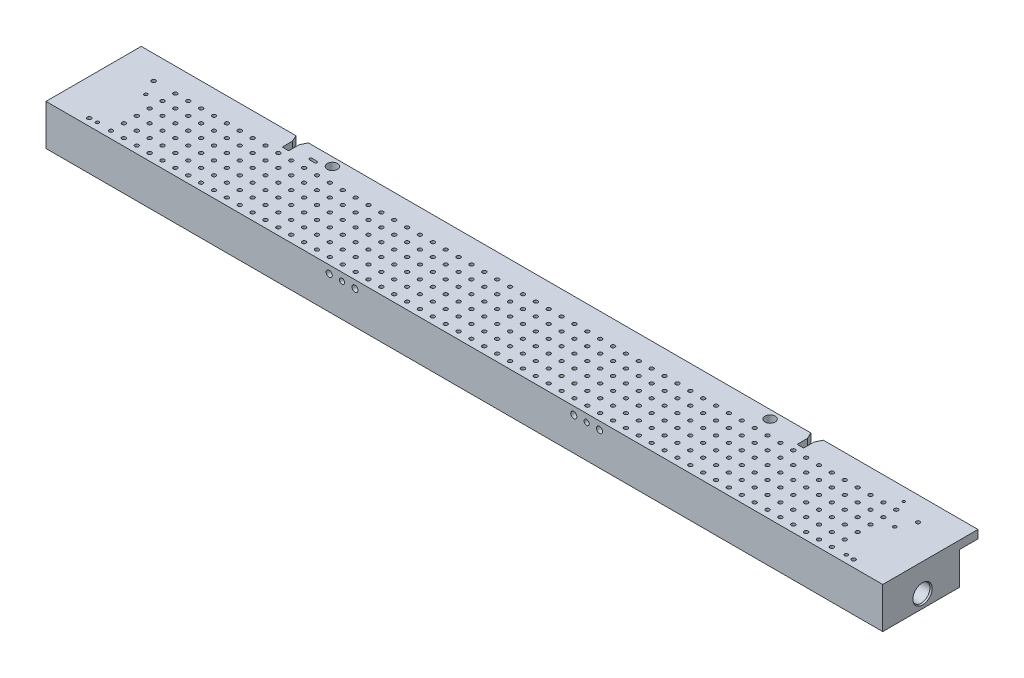
SolidWorks part; units mm, degrees
ref_plane "Front Plane" through (0, 0, 0) normal (0, 0, 1) x (1, 0, 0)
ref_plane "Top Plane" through (0, 0, 0) normal (0, 1, 0) x (1, 0, 0)
ref_plane "Right Plane" through (0, 0, 0) normal (1, 0, 0) x (0, 0, -1)
sketch "Sketch1" plane through (0, 0, 0) normal (0, 1, 0) x (1, 0, 0)
  line L1 (-55.7213, 28.6477) -> (594.2787, 28.6477)
  line L2 (-55.7213, 28.6477) -> (-55.7213, -85.6523)
  line L3 (-55.7213, -85.6523) -> (594.2787, -85.6523)
  line L4 (594.2787, 28.6477) -> (594.2787, -85.6523)
  dimension "D1" = 650
  dimension "D2" = 114.3
extrude "Boss-Extrude1" add sketch "Sketch1" against normal blind 31.75
hole_wizard "Hole2" positions "Sketch5" profile "Sketch4" legacy
sketch "Sketch5" plane through (0, 0, 0) normal (0, 1, 0) x (1, 0, 0)
  line L0 (-55.7213, 28.6477) -> (-55.7213, -85.6523) construction
  line L1 (-55.7213, -85.6523) -> (594.2787, -85.6523) construction
  point P0 (99.2787, -18.1523)
  point P2 (439.2787, -18.1523)
  dimension "D1" = 155
  dimension "D2" = 340
  dimension "D3" = 67.5
  dimension "D4" = 67.5
sketch "Sketch4" plane through (99.2787, 0, 18.1523) normal (1, 0, 0) x (0, 0, 1)
  line L0 (0, 0) -> (0, 15.875)
  line L1 (0, 15.875) -> (3.9815, 15.875)
  line L2 (3.9815, 15.875) -> (3.9815, 0)
  line L3 (3.9815, 0) -> (0, 0)
  line L4 (0, 110) -> (0, -10) construction
  dimension "Diameter" = 7.9629
  dimension "Depth" = 15.875
hole_wizard "Hole4" positions "Sketch12" profile "Sketch11" legacy
sketch "Sketch12" plane through (0, 0, 0) normal (0, 1, 0) x (1, 0, 0)
  line L0 (-55.7213, -85.6523) -> (594.2787, -85.6523) construction
  line L1 (269.2787, 45.076) -> (269.2787, -110.0283) construction
  point P0 (69.2787, -22.1523)
  point P2 (469.2787, -22.1523)
  dimension "D1" = 200
  dimension "D2" = 200
  dimension "D3" = 63.5
  dimension "D4" = 63.5
sketch "Sketch11" plane through (69.2787, 0, 22.1523) normal (1, 0, 0) x (0, 0, 1)
  line L0 (0, 0) -> (0, 15.875)
  line L1 (0, 15.875) -> (2.5, 15.875)
  line L2 (2.5, 15.875) -> (2.5, 0)
  line L3 (2.5, 0) -> (0, 0)
  line L4 (0, 110) -> (0, -10) construction
  dimension "Diameter" = 5
  dimension "Depth" = 15.875
hole_wizard "Hole6" positions "Sketch16" profile "Sketch15" legacy
sketch "Sketch16" plane through (0, 0, 0) normal (0, 1, 0) x (1, 0, 0)
  line L1 (-55.7213, -85.6523) -> (594.2787, -85.6523) construction
  line L2 (269.2787, -103.4746) -> (269.2787, 56.727) construction
  point P2 (-27.6213, -80.1523)
  point P4 (566.1787, -80.1523)
  point P22 (-27.6213, -30.1523)
  point P25 (566.1787, -30.1523)
  dimension "D1" = 296.9
  dimension "D2" = 296.9
  dimension "D3" = 55.5
  dimension "D5" = 5.5
  dimension "D6" = 5.5
sketch "Sketch15" plane through (-27.6213, 0, 80.1523) normal (1, 0, 0) x (0, 0, 1)
  line L0 (0, 0) -> (0, 5)
  line L1 (0, 5) -> (1.5, 5)
  line L2 (1.5, 5) -> (1.5, 0)
  line L3 (1.5, 0) -> (0, 0)
  line L4 (0, 110) -> (0, -10) construction
  dimension "Diameter" = 3
  dimension "Depth" = 5
hole_wizard "Hole7" positions "Sketch18" profile "Sketch17" legacy
sketch "Sketch18" plane through (0, 0, 0) normal (0, 1, 0) x (1, 0, 0)
  line L0 (-55.7213, -85.6523) -> (594.2787, -85.6523) construction
  line L1 (269.2787, 54.0915) -> (269.2787, -171.9418) construction
  point P0 (279.2787, -80.1523)
  dimension "D2" = 10
  dimension "D1" = 5.5
sketch "Sketch17" plane through (279.2787, 0, 80.1523) normal (1, 0, 0) x (0, 0, 1)
  line L0 (0, 0) -> (0, 30)
  line L1 (0, 30) -> (1.5, 30)
  line L2 (1.5, 30) -> (1.5, 0)
  line L3 (1.5, 0) -> (0, 0)
  line L4 (0, 110) -> (0, -10) construction
  dimension "Diameter" = 3
  dimension "Depth" = 30
sketch "Sketch19" plane through (0, 0, 0) normal (0, 1, 0) x (1, 0, 0)
  line L0 (277.7787, -80.1523) -> (50277.7787, -80.1523) construction
  line L1 (279.2787, -80.1523) -> (279.2787, 49919.8477) construction
  line L2 (269.2787, 97.4934) -> (269.2787, -133.194) construction
  circle A0 centre (279.2787, -80.1523) radius 1.5 construction
  dimension "D1" = 10
pattern_linear "LPattern2" count 28 spacing 10 along (1, 0, 0) count 6 spacing 10 along (0, 0, -1) of "Hole7"
hole_wizard "Hole12" positions "Sketch34" profile "Sketch33" legacy
sketch "Sketch34" plane through (0, 0, 0) normal (0, 1, 0) x (1, 0, 0)
  line L0 (-199722.2213, -80.1523) -> (250277.7787, -80.1523) construction
  line L1 (269.2787, 97.4934) -> (269.2787, -133.194) construction
  point P0 (269.2787, -80.1523)
sketch "Sketch33" plane through (269.2787, 0, 80.1523) normal (1, 0, 0) x (0, 0, 1)
  line L0 (0, 0) -> (0, 30)
  line L1 (0, 30) -> (1.5, 30)
  line L2 (1.5, 30) -> (1.5, 0)
  line L3 (1.5, 0) -> (0, 0)
  line L4 (0, 110) -> (0, -10) construction
  dimension "Diameter" = 3
  dimension "Depth" = 30
pattern_linear "LPattern3" count 29 spacing 10 along (-1, 0, 0) count 6 spacing 10 along (0, 0, -1) of "Hole12"
sketch "Sketch35" plane through (0, 0, 85.6523) normal (0, 0, 1) x (1, 0, 0)
  line L0 (269.2787, 71.714) -> (269.2787, -64.9274) construction
  line L1 (-55.7213, -31.75) -> (-55.7213, 0) construction
  dimension "D1" = 325
hole_wizard "Hole13" positions "Sketch37" profile "Sketch36" legacy
sketch "Sketch37" plane through (0, 0, 85.6523) normal (0, 0, 1) x (1, 0, 0)
  line L0 (269.2787, 71.714) -> (269.2787, -64.9274) construction
  line L1 (-199722.2213, 0) -> (250277.7787, 0) construction
  point P0 (184.2787, -6)
  point P2 (164.2787, -6)
  point P4 (374.2787, -6)
  point P6 (354.2787, -6)
  dimension "D1" = 105
  dimension "D2" = 85
  dimension "D3" = 105
  dimension "D4" = 85
  dimension "D5" = 6
  dimension "D6" = 6
  dimension "D7" = 6
  dimension "D8" = 6
sketch "Sketch36" plane through (184.2787, -6, 85.6523) normal (1, 0, 0) x (0, -1, 0)
  line L0 (0, 0) -> (0, 12)
  line L1 (0, 12) -> (2.3813, 12)
  line L2 (2.3813, 12) -> (2.3813, 0)
  line L3 (2.3813, 0) -> (0, 0)
  line L4 (0, 110) -> (0, -10) construction
  dimension "Diameter" = 4.7625
  dimension "Depth" = 12
hole_wizard "#10-32 Tapped Hole1" positions "Sketch40" profile "Sketch38" tap size "#10-32" standard "ANSI Inch"
sketch "Sketch40" plane through (0, 0, 85.6523) normal (0, 0, 1) x (1, 0, 0)
  line L0 (269.2787, 71.714) -> (269.2787, -64.9274) construction
  line L1 (-199722.2213, 0) -> (250277.7787, 0) construction
  point P0 (174.2787, -6)
  point P2 (364.2787, -6)
  dimension "D1" = 95
  dimension "D2" = 95
  dimension "D3" = 6
  dimension "D4" = 6
sketch "Sketch38" plane through (174.2787, -6, 85.6523) normal (1, 0, 0) x (0, -1, 0)
  line L0 (0, 0) -> (0, 16.4533)
  line L1 (0, 16.4533) -> (2.0193, 15.24)
  line L2 (2.0193, 15.24) -> (2.0193, 0)
  line L5 (2.0193, 0) -> (0, 0)
  line L10 (0, 16.4533) -> (-2.0193, 15.24) construction
  line L11 (0, -6.35) -> (0, 107.95) construction
  dimension "Tap Drill Dia." = 4.0386
  dimension "Tap Drill Depth" = 15.24
  dimension "Drill Angle" = 118
cosmetic thread "Hole Thread1" parameters "D1"=12.7, "D2"=4.826
cosmetic thread "Hole Thread2" parameters "D1"=12.7, "D2"=4.826
sketch "Sketch41" plane through (0, -31.75, 0) normal (0, -1, 0) x (1, 0, 0)
  line L1 (-15.7213, 81.1523) -> (554.2787, 81.1523)
  line L2 (-15.7213, 81.1523) -> (-15.7213, 26.1523)
  line L3 (-15.7213, 26.1523) -> (554.2787, 26.1523)
  line L4 (554.2787, 81.1523) -> (554.2787, 26.1523)
  line L5 (-55.7213, 85.6523) -> (594.2787, 85.6523) construction
  line L6 (-55.7213, -28.6477) -> (-55.7213, 85.6523) construction
  line L7 (594.2787, 85.6523) -> (594.2787, -28.6477) construction
  dimension "D1" = 4.5
  dimension "D2" = 55
  dimension "D3" = 40
  dimension "D4" = 40
sketch "Sketch51" plane through (594.2787, 0, 0) normal (1, 0, 0) x (0, 0, -1)
  line L0 (-85.6523, -31.75) -> (28.6477, -31.75) construction
  line L1 (28.6477, 0) -> (-11.6523, 0)
  line L2 (28.6477, 0) -> (28.6477, -31.75)
  line L3 (28.6477, -31.75) -> (-11.6523, -31.75)
  line L4 (-11.6523, 0) -> (-11.6523, -31.75)
  dimension "D1" = 40.3
extrude "Cut-Extrude8" cut sketch "Sketch51" against normal blind 40000
sketch "Sketch52" plane through (594.2787, 0, 0) normal (1, 0, 0) x (0, 0, -1)
  line L1 (-11.6523, -31.75) -> (-21.6523, -31.75)
  line L2 (-11.6523, -31.75) -> (-11.6523, -6.35)
  line L3 (-11.6523, -6.35) -> (-21.6523, -6.35)
  line L4 (-21.6523, -31.75) -> (-21.6523, -6.35)
  dimension "D1" = 10
  dimension "D2" = 25.4
extrude "Cut-Extrude9" cut sketch "Sketch52" against normal blind 40000
sketch "Sketch55" plane through (-55.7213, 0, 0) normal (-1, 0, 0) x (0, 0, 1)
  line L0 (21.6523, -31.75) -> (85.6523, -31.75) construction
  line L1 (21.6523, -6.35) -> (25.1523, -6.35)
  line L2 (21.6523, -6.35) -> (21.6523, -31.75)
  line L3 (21.6523, -31.75) -> (25.1523, -31.75)
  line L4 (25.1523, -6.35) -> (25.1523, -31.75)
  dimension "D1" = 3.5
extrude "Cut-Extrude10" cut sketch "Sketch55" against normal blind 40000
sketch "Sketch56" plane through (594.2787, 0, 0) normal (1, 0, 0) x (0, 0, -1)
  line L1 (-25.1523, -31.75) -> (-26.1523, -31.75)
  line L2 (-25.1523, -31.75) -> (-25.1523, -6.35)
  line L3 (-25.1523, -6.35) -> (-26.1523, -6.35)
  line L4 (-26.1523, -31.75) -> (-26.1523, -6.35)
  dimension "D1" = 25.4
  dimension "D2" = 1
extrude "Cut-Extrude11" cut sketch "Sketch56" against normal blind 40000
sketch "Sketch57" plane through (0, -31.75, 0) normal (0, -1, 0) x (-1, 0, 0)
  line L1 (15.7213, -81.1523) -> (-554.2787, -81.1523)
  line L2 (15.7213, -81.1523) -> (15.7213, -30.3716)
  line L3 (15.7213, -30.3716) -> (-554.2787, -30.3716)
  line L4 (-554.2787, -81.1523) -> (-554.2787, -30.3716)
extrude "Cut-Extrude12" cut sketch "Sketch57" against normal blind 10
sketch "Sketch58" plane through (0, -31.75, 0) normal (0, -1, 0) x (-1, 0, 0)
  line L0 (-557.2787, -84.1523) -> (18.7213, -84.1523)
  line L1 (18.7213, -84.1523) -> (18.7213, -27.3716)
  line L3 (18.7213, -27.3716) -> (-557.2787, -27.3716)
  line L4 (-557.2787, -84.1523) -> (-557.2787, -27.3716)
  line L5 (15.7213, -30.3716) -> (-554.2787, -30.3716) construction
  dimension "D1" = 3
extrude "Cut-Extrude13" cut sketch "Sketch58" against normal blind 3.5
fillet "Fillet1" radius 3.18 8 edges at (554.2787, -25, 30.3716) (557.2787, -30, 27.3716) (554.2787, -25, 81.1523) (-15.7213, -25, 30.3716) (-15.7213, -25, 81.1523) (557.2787, -30, 84.1523) (-18.7213, -30, 84.1523) (-18.7213, -30, 27.3716)
sketch "Sketch60" plane through (0, -6.35, 0) normal (0, -1, 0) x (-1, 0, 0)
  line L0 (-594.2787, -11.6523) -> (55.7213, -11.6523) construction
  line L1 (-66.7787, -24.6523) -> (-71.7787, -24.6523)
  line L2 (-66.7787, -24.6523) -> (-66.7787, -11.6523)
  line L3 (-66.7787, -11.6523) -> (-71.7787, -11.6523)
  line L4 (-71.7787, -24.6523) -> (-71.7787, -11.6523)
extrude "Cut-Extrude17" cut sketch "Sketch60" against normal blind 10
sketch "Sketch61" plane through (0, -6.35, 0) normal (0, -1, 0) x (-1, 0, 0)
  line L0 (-594.2787, -11.6523) -> (-71.7787, -11.6523) construction
  line L1 (-466.7787, -24.6523) -> (-471.7787, -24.6523)
  line L2 (-466.7787, -24.6523) -> (-466.7787, -11.6523)
  line L3 (-466.7787, -11.6523) -> (-471.7787, -11.6523)
  line L4 (-471.7787, -24.6523) -> (-471.7787, -11.6523)
  circle A0 centre (-469.2787, -22.1523) radius 2.5 construction
  dimension "D2" = 2.5
  dimension "D1" = 2.5
  dimension "D3" = 5
extrude "Cut-Extrude18" cut sketch "Sketch61" against normal blind 10
chamfer "Chamfer3" distance 5 angle 25 1 edges at (66.7787, -3.175, 11.6523)
chamfer "Chamfer4" distance 5 angle 25 1 edges at (71.7787, -3.175, 11.6523)
chamfer "Chamfer5" distance 5 angle 25 1 edges at (471.7787, -3.175, 11.6523)
chamfer "Chamfer6" distance 5 angle 25 1 edges at (466.7787, -3.175, 11.6523)
hole_wizard "1/4 NPT Tapped Hole1" positions "Sketch65" profile "Sketch64" size "1/4" standard "ANSI Inch"
sketch "Sketch65" plane through (594.2787, 0, 0) normal (1, 0, 0) x (0, 0, -1)
  line L0 (-81.1523, -31.75) -> (-26.1523, -31.75) construction
  point P0 (-54.7527, -21.75)
  dimension "D1" = 10
sketch "Sketch64" plane through (594.2787, -21.75, 54.7527) normal (0, 1, 0) x (0, 0, -1)
  line L0 (0, 0) -> (0, 50.4123)
  line L1 (5.5626, 47.07) -> (0, 50.4123)
  line L2 (-5.5626, 47.07) -> (0, 50.4123) construction
  line L3 (5.5626, 47.07) -> (5.5626, 10.02)
  line L4 (5.5626, 10.02) -> (6.5909, 10.02)
  line L5 (6.5909, 10.02) -> (6.858, 1.0999)
  line L6 (6.858, 1.0999) -> (7.493, 0)
  line L7 (7.493, 0) -> (0, 0)
  line L8 (0, -6.35) -> (0, 107.95) construction
  line L9 (-6.858, 1.0999) -> (-7.493, 0) construction
  line L11 (-5.5626, 10.02) -> (-6.5909, 10.02) construction
  line L12 (-6.5909, 10.02) -> (-6.858, 1.0999) construction
  dimension "Tap Drill Dia." = 11.1252
  dimension "Tap Drill Depth" = 47.07
  dimension "Thread Dia." = 13.716
  dimension "Thread Angle" = 3.43
  dimension "Thread Depth" = 10.02
  dimension "C'Sink Dia." = 14.986
  dimension "C'Sink Angle" = 60
  dimension "Drill Angle" = 118
sketch "Sketch67" plane through (0, 0, 0) normal (0, 1, 0) x (1, 0, 0)
  line L0 (-55.7213, -85.6523) -> (594.2787, -85.6523) construction
  line L1 (269.2787, 97.4934) -> (269.2787, -133.194) construction
  line L2 (85.8787, -21.6523) -> (89.8787, -21.6523) construction
  line L3 (85.8787, -20.6523) -> (89.8787, -20.6523)
  line L4 (85.8787, -22.6523) -> (89.8787, -22.6523)
  circle A0 centre (546.6787, -21.6523) radius 1
  arc A1 (85.8787, -20.6523) -> (85.8787, -22.6523) centre (85.8787, -21.6523) ccw
  arc A2 (89.8787, -22.6523) -> (89.8787, -20.6523) centre (89.8787, -21.6523) ccw
  point P8 (87.8787, -21.6523)
  dimension "D1" = 64
  dimension "D3" = 181.4
  dimension "D2" = 277.4
extrude "Cut-Extrude19" cut sketch "Sketch67" against normal blind 5
hole_wizard "M3x0.5 Tapped Hole2" positions "Sketch73" profile "Sketch72" tap size "M3x0.5" standard "ANSI Metric"
sketch "Sketch73" plane through (0, 0, 0) normal (0, 1, 0) x (1, 0, 0)
  line L0 (269.2787, 97.4934) -> (269.2787, -133.194) construction
  line L2 (-55.7213, -85.6523) -> (594.2787, -85.6523) construction
  point P0 (-21.6213, -42.2053)
  point P8 (-21.6213, -79.8803)
  point P13 (560.1787, -42.2053)
  point P19 (560.1787, -79.8803)
  dimension "D1" = 290.9
  dimension "D2" = 5.772
  dimension "D3" = 43.447
  dimension "D4" = 290.9
  dimension "D5" = 5.772
  dimension "D6" = 43.447
sketch "Sketch72" plane through (-21.6213, 0, 42.2053) normal (1, 0, 0) x (0, 0, 1)
  line L0 (0, 0) -> (0, 10.7511)
  line L1 (0, 10.7511) -> (1.25, 10)
  line L2 (1.25, 10) -> (1.25, 0)
  line L5 (1.25, 0) -> (0, 0)
  line L10 (0, 10.7511) -> (-1.25, 10) construction
  line L11 (0, -6.35) -> (0, 107.95) construction
  dimension "Tap Drill Dia." = 2.5
  dimension "Tap Drill Depth" = 10
  dimension "Drill Angle" = 118
cosmetic thread "Hole Thread4" parameters "D1"=6, "D2"=3
cosmetic thread "Hole Thread5" parameters "D1"=6, "D2"=3
cosmetic thread "Hole Thread6" parameters "D1"=6, "D2"=3
cosmetic thread "Hole Thread7" parameters "D1"=6, "D2"=3
